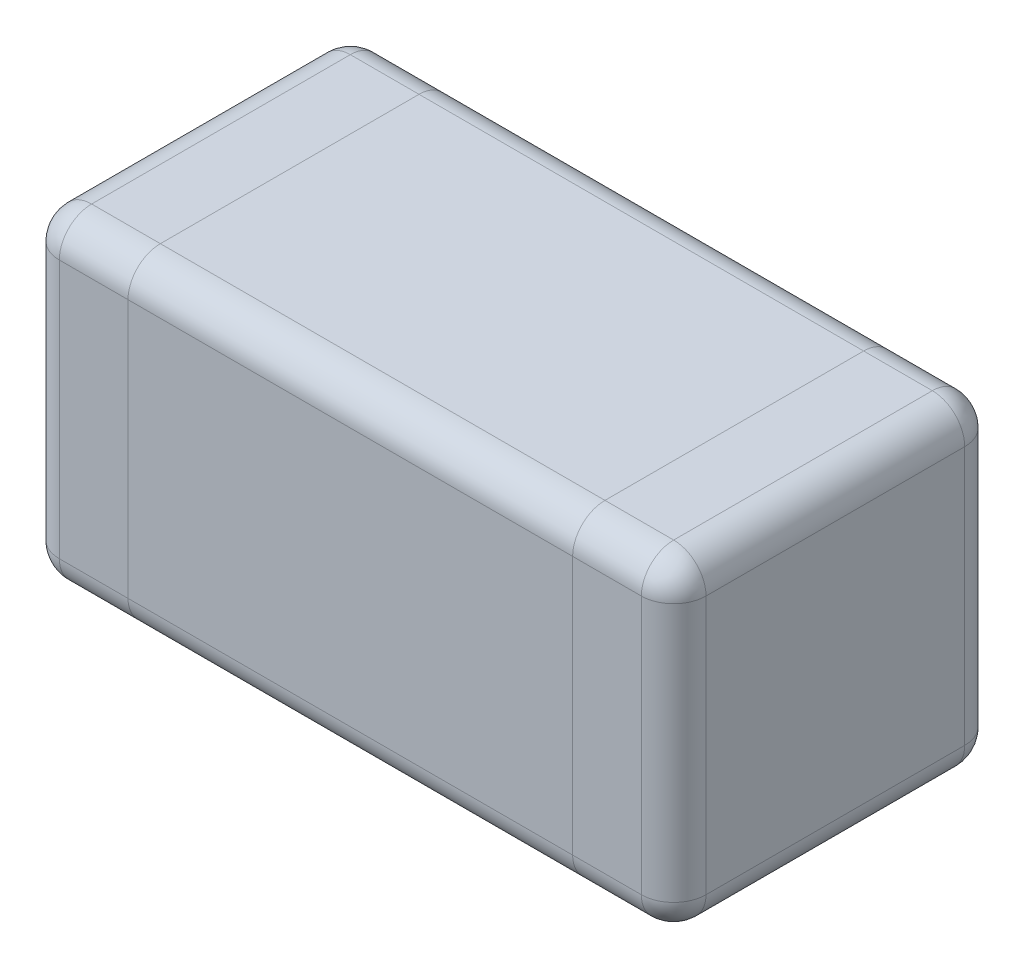
SolidWorks part; units mm, degrees
ref_plane "Plano frontal" through (0, 0, 0) normal (0, 0, 1) x (1, 0, 0)
ref_plane "Plano superior" through (0, 0, 0) normal (0, 1, 0) x (1, 0, 0)
ref_plane "Plano direito" through (0, 0, 0) normal (1, 0, 0) x (0, 0, -1)
sketch "Esboço1" plane through (0, 0, 0) normal (0, 1, 0) x (1, 0, 0)
  line L1 (0, 0) -> (1.6, 0)
  line L2 (0, 0) -> (0, 0.8)
  line L3 (0, 0.8) -> (1.6, 0.8)
  line L4 (1.6, 0) -> (1.6, 0.8)
  dimension "L1" = 1.6
  dimension "W" = 0.8
extrude "Ressalto-extrusão1" add sketch "Esboço1" along normal blind 0.8
fillet "Filete2" radius 0.08 12 edges at (1.6, 0.4, 0) (1.6, 0.4, -0.8) (0, 0.4, -0.8) (0, 0.4, 0) (0.8, 0, 0) (1.6, 0, -0.4) (0.8, 0, -0.8) (0, 0, -0.4) (0.8, 0.8, -0.8) (1.6, 0.8, -0.4) (0.8, 0.8, 0) (0, 0.8, -0.4)
sketch "Esboço2" plane through (0, 0, 0) normal (0, 0, 1) x (1, 0, 0)
  line L0 (0.25, 0) -> (0.25, 0.8)
  line L1 (0, 0) -> (1.6, 0) construction
  line L2 (0, 0.8) -> (1.6, 0.8) construction
  line L3 (0.8, 0.8) -> (0.8, 0) construction
  line L4 (1.35, 0) -> (1.35, 0.8)
  line L5 (0, 0.08) -> (0, 0.72) construction
  dimension "L2" = 0.25
split line "Linha de divisão1"
